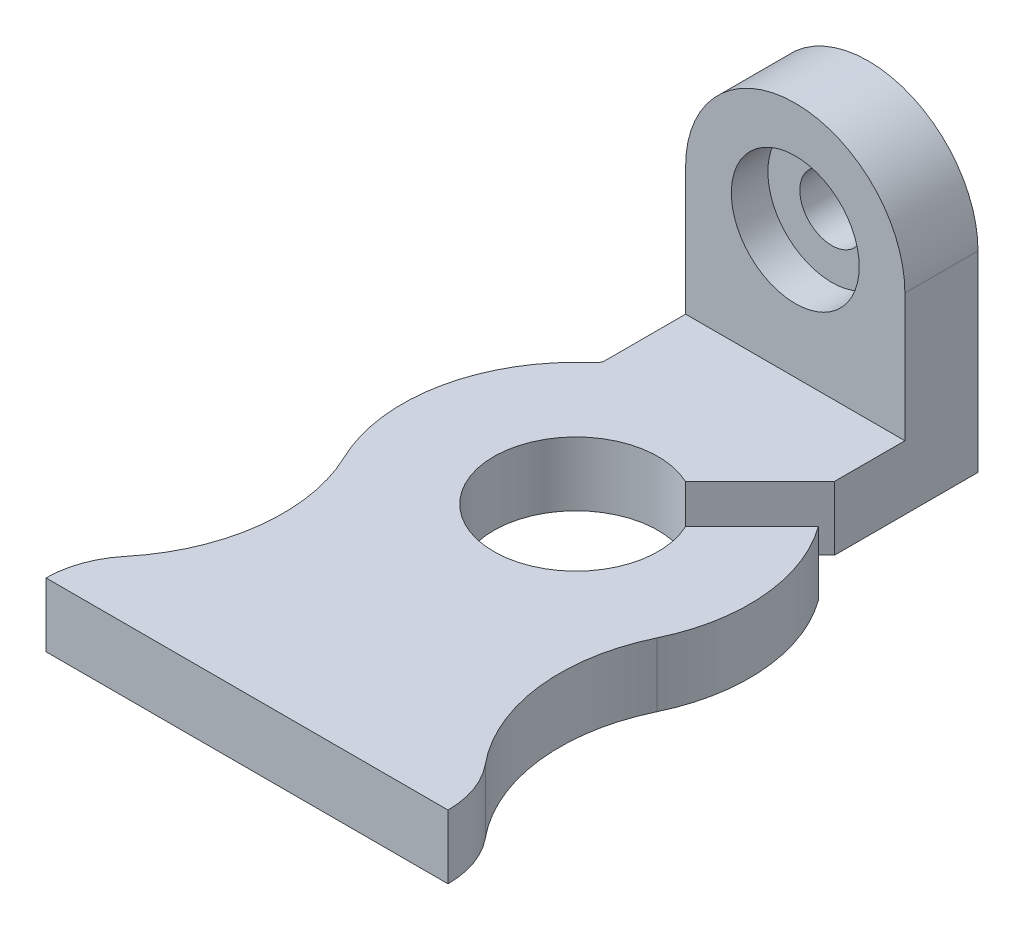
SolidWorks part; units mm, degrees
ref_plane "Front Plane" through (0, 0, 0) normal (0, 0, 1) x (1, 0, 0)
ref_plane "Top Plane" through (0, 0, 0) normal (0, 1, 0) x (1, 0, 0)
ref_plane "Right Plane" through (0, 0, 0) normal (1, 0, 0) x (0, 0, -1)
sketch "Sketch1" plane through (0, 0, 0) normal (0, 1, 0) x (1, 0, 0)
  line L0 (-69.85, 0) -> (69.85, 0)
  line L1 (0, 0) -> (0, 215.9) construction
  line L2 (0, 215.9) -> (0, 268.6232) construction
  line L3 (0, 0) -> (0, -108.4911) construction
  line L4 (-38.1, 215.9) -> (38.1, 215.9)
  line L5 (38.1, 215.9) -> (38.1, 162.5558)
  line L6 (-38.1, 215.9) -> (-38.1, 162.5558)
  arc A0 (69.85, 0) -> (62.593, 20.2029) centre (38.1, 0) ccw
  circle A1 centre (0, 114.3) radius 28.575
  arc A2 (54.359, 88.1427) -> (39.2112, 160.143) centre (0, 114.3) ccw
  arc A3 (39.2112, 160.143) -> (38.1, 162.5558) centre (41.275, 162.5558) cw
  arc A4 (-54.359, 88.1427) -> (-62.593, 20.2029) centre (-111.579, 60.6086) cw
  arc A5 (54.359, 88.1427) -> (62.593, 20.2029) centre (111.579, 60.6086) ccw
  arc A6 (-39.2112, 160.143) -> (-38.1, 162.5558) centre (-41.275, 162.5558) ccw
  arc A7 (-54.359, 88.1427) -> (-39.2112, 160.143) centre (0, 114.3) cw
  arc A8 (-69.85, 0) -> (-62.593, 20.2029) centre (-38.1, 0) cw
  dimension "D3" = 3.175
  dimension "D6" = 57.15
  dimension "D7" = 60.325
  dimension "D8" = 63.5
  dimension "D9" = 31.75
  dimension "D10" = 41.729
  dimension "D1" = 69.85
  dimension "D2" = 38.1
  dimension "D4" = 215.9
  dimension "D5" = 114.3
extrude "Boss-Extrude1" add sketch "Sketch1" along normal blind 22.225
sketch "Sketch3" plane through (0, 0, -215.9) normal (0, 0, -1) x (-1, 0, 0)
  line L1 (38.1, 22.225) -> (-38.1, 22.225)
  line L2 (38.1, 22.225) -> (38.1, 66.675)
  line L3 (38.1, 66.675) -> (-38.1, 66.675)
  line L4 (-38.1, 22.225) -> (-38.1, 66.675)
  circle A0 centre (0, 66.675) radius 11.1125
  arc A1 (38.1, 66.675) -> (-38.1, 66.675) centre (0, 66.675) ccw
  line M4 (38.1, 22.225) -> (-38.1, 22.225)
  dimension "D2" = 76.2
  dimension "D3" = 22.225
  dimension "D1" = 44.45
extrude "Boss-Extrude2" add sketch "Sketch3" against normal blind 25.4 contours L3 A1 A0 | A0 L3 L4 L2 M4
sketch "Sketch4" plane through (0, 0, -190.5) normal (0, 0, 1) x (1, 0, 0)
  circle A0 centre (0, 66.675) radius 22.225
  dimension "D1" = 44.45
extrude "Cut-Extrude1" cut sketch "Sketch4" against normal blind 12.7
sketch "Sketch5" plane through (0, 22.225, 0) normal (0, 1, 0) x (1, 0, 0)
  line L0 (0, 114.3) -> (51.5933, 165.8933)
  line L1 (0, 114.3) -> (60.325, 114.3) construction
  line L2 (44.7683, 172.7183) -> (58.4183, 159.0683)
  line L3 (58.4183, 159.0683) -> (6.825, 107.475)
  line L4 (6.825, 107.475) -> (-6.825, 121.125)
  line L5 (44.7683, 172.7183) -> (-6.825, 121.125)
  arc A0 (54.359, 88.1427) -> (39.2113, 160.143) centre (0, 114.3) ccw construction
  arc M15 (54.359, 88.1427) -> (39.2113, 160.143) centre (0, 114.3) ccw
  arc M16 (39.2113, 160.143) -> (38.1, 162.5558) centre (41.275, 162.5558) cw
  line M17 (38.1, 162.5558) -> (38.1, 190.5)
  circle M18 centre (0, 114.3) radius 28.575
  dimension "D1" = 72.9639
  dimension "D2" = 9.652
  dimension "D3" = 45
extrude "Cut-Extrude2" cut sketch "Sketch5" against normal through all contours L2 L5 L0 M17 M16 M15 | L5 L0 M17 M18 M15 M16 | L3 L2 L0 M15 | L3 L0 M15 M18
